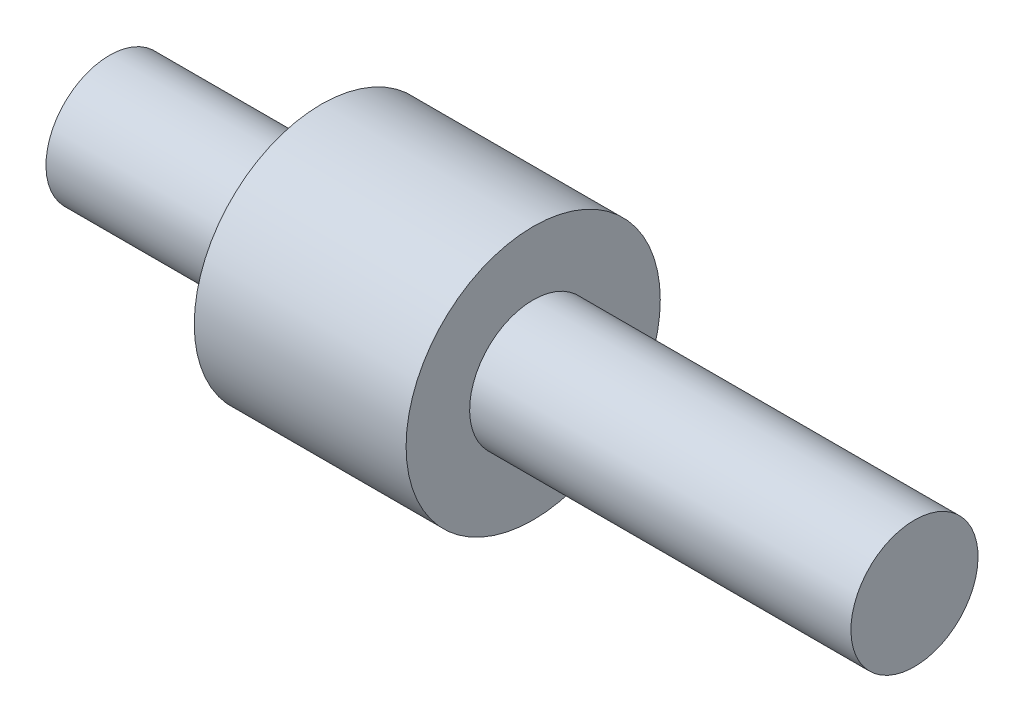
SolidWorks part; units mm, degrees
ref_plane "Plan de face" through (0, 0, 0) normal (0, 0, 1) x (1, 0, 0)
ref_plane "Plan de dessus" through (0, 0, 0) normal (0, 1, 0) x (1, 0, 0)
ref_plane "Plan de droite" through (0, 0, 0) normal (1, 0, 0) x (0, 0, -1)
sketch "Esquisse1" plane through (0, 0, 0) normal (0, 0, 1) x (1, 0, 0)
  line L0 (0, 0) -> (0, 1.5)
  line L1 (0, 1.5) -> (5, 1.5)
  line L2 (5, 1.5) -> (5, 3)
  line L3 (5, 3) -> (10, 3)
  line L4 (10, 3) -> (10, 1.5)
  line L5 (10, 1.5) -> (19, 1.5)
  line L6 (19, 1.5) -> (19, 0)
  line L7 (19, 0) -> (0, 0)
  dimension "D1" = 1.5
  dimension "D2" = 1.5
  dimension "D3" = 3
  dimension "D4" = 9
  dimension "D5" = 5
  dimension "D6" = 5
revolve "Révolution1" add sketch "Esquisse1" angle 360 about L7
